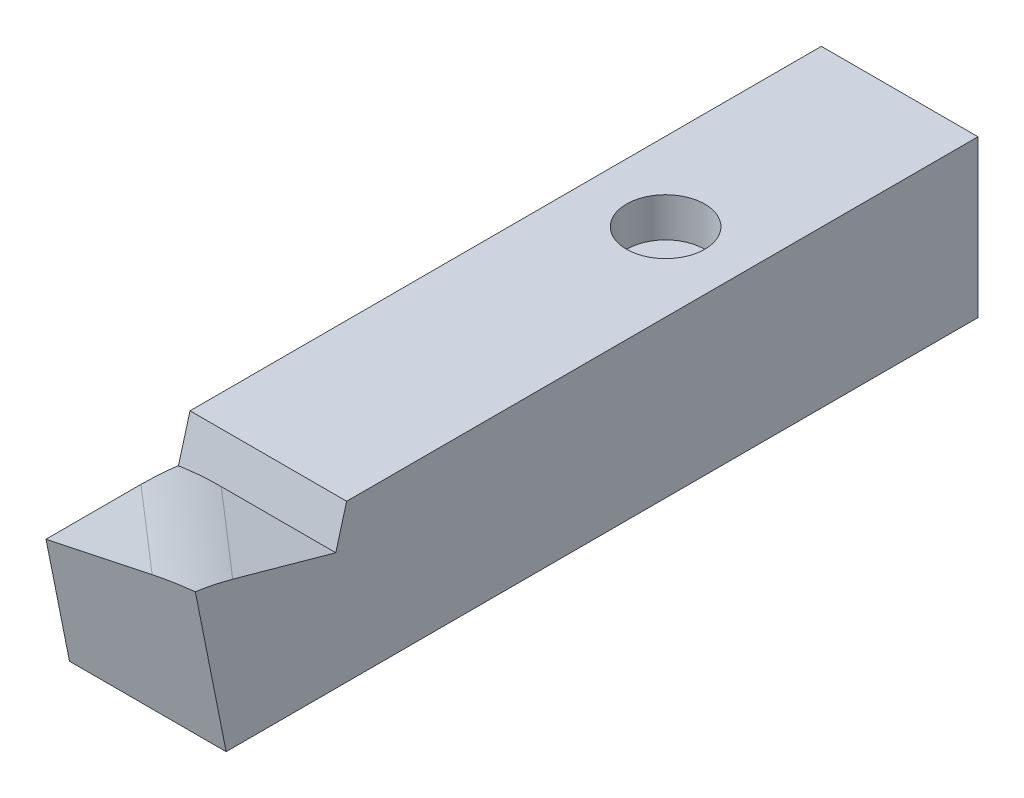
SolidWorks part; units mm, degrees
material "HSS"
ref_plane "Front Plane" through (0, 0, 0) normal (0, 0, 1) x (1, 0, 0)
ref_plane "Top Plane" through (0, 0, 0) normal (0, 1, 0) x (1, 0, 0)
ref_plane "Right Plane" through (0, 0, 0) normal (1, 0, 0) x (0, 0, -1)
sketch "Sketch1" plane through (0, 0, 0) normal (0, 0, 1) x (1, 0, 0)
  line L1 (-10, 10) -> (10, 10)
  line L2 (-10, 10) -> (-10, -10)
  line L3 (-10, -10) -> (10, -10)
  line L4 (10, 10) -> (10, -10)
  line L5 (-10, 10) -> (10, -10) construction
  line L6 (-10, -10) -> (10, 10) construction
  point P0 (0, 0)
  dimension "D1" = 20
  dimension "D2" = 20
extrude "Boss-Extrude1" add sketch "Sketch1" against normal blind 100
sketch "Sketch4" plane through (10, 0, 0) normal (1, 0, 0) x (0, 0, -1)
  line L0 (0, 10) -> (18, 5)
  line L1 (18, 5) -> (19.3889, 10)
  line L2 (100, 10) -> (0, 10) construction
  line L3 (0, 10) -> (19.3889, 10)
  line L4 (0, 10) -> (4, -10)
  line L5 (100, -10) -> (0, -10) construction
  line L6 (4, -10) -> (0, -10)
  line L7 (0, -10) -> (0, 10)
  line M2 (0, 10) -> (0, -10)
  line M3 (0, -10) -> (100, -10)
  line M5 (100, 10) -> (0, 10)
  dimension "D1" = 5
  dimension "D2" = 4
  dimension "D3" = 18
extrude "Cut-Extrude3" cut sketch "Sketch4" against normal blind 20 contours L0 L1 M5 | L4 M2 M3
sketch "Sketch5" plane through (0, 0, 0) normal (0, 0, 1) x (1, 0, 0)
  line L0 (-10, 5) -> (10, 10)
  line L2 (-10, 10) -> (-10, -10) construction
  line L3 (-10, 5) -> (-10, 10)
  line L4 (-10, 10) -> (10, 10)
  dimension "D1" = 5
extrude "Cut-Extrude4" cut sketch "Sketch5" against normal blind 18
fillet "Fillet3" radius 20 1 edges at (0, 7.5, -9)
sketch "Sketch6" plane through (0, 10, 0) normal (0, 1, 0) x (1, 0, 0)
  circle A0 centre (0, 70.1147) radius 5
  dimension "D1" = 10
extrude "Cut-Extrude5" cut sketch "Sketch6" against normal blind 5
